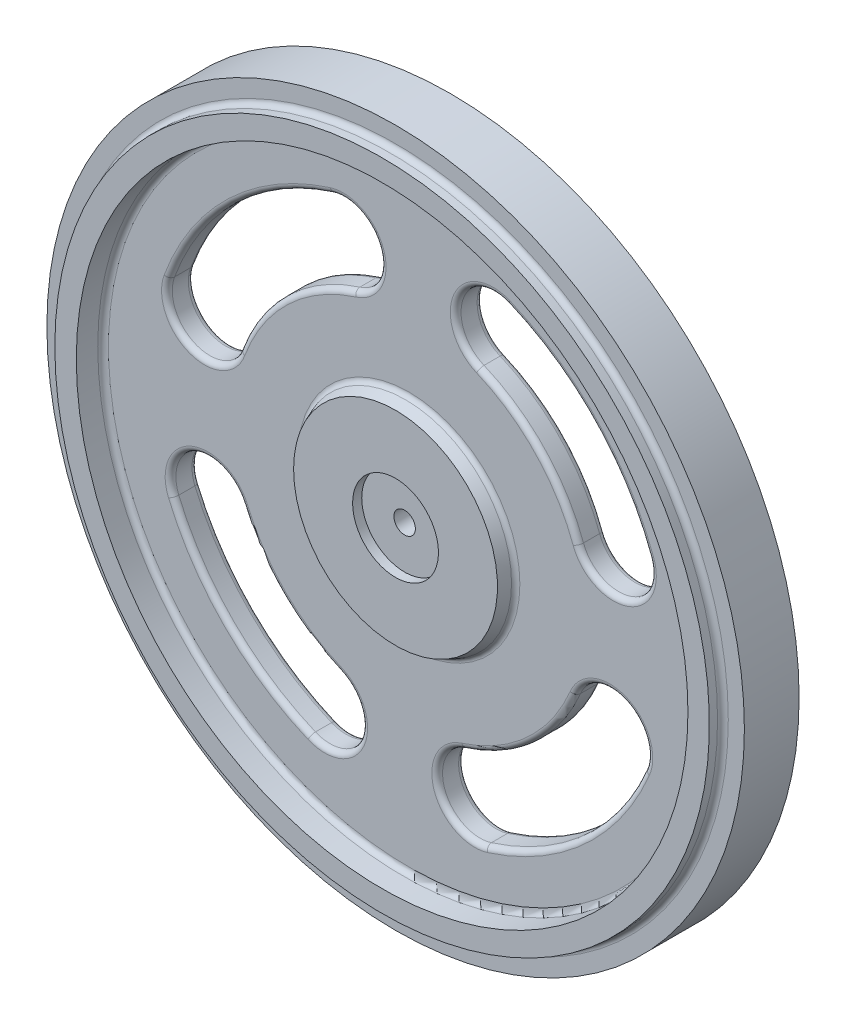
SolidWorks part; units mm, degrees
ref_plane "Front Plane" through (0, 0, 0) normal (0, 0, 1) x (1, 0, 0)
ref_plane "Top Plane" through (0, 0, 0) normal (0, 1, 0) x (1, 0, 0)
ref_plane "Right Plane" through (0, 0, 0) normal (1, 0, 0) x (0, 0, -1)
sketch "Sketch1" plane through (0, 0, 0) normal (1, 0, 0) x (0, 0, -1)
  line L0 (25, 0) -> (-25, 0) construction
  line L1 (-2.55, 32.5) -> (-2.55, 30.5)
  line L2 (-3.81, 28.5) -> (-3.81, 30.5)
  line L3 (-2.55, 32.5) -> (2.55, 32.5)
  line L4 (3.69, 2.75) -> (3.69, 4.5)
  line L5 (-2.55, 30.5) -> (-3.81, 30.5)
  line L6 (2.55, 32.5) -> (2.55, 30.5)
  line L7 (2.55, 30.5) -> (3.69, 30.5)
  line L8 (-3.81, 28.5) -> (-1.31, 28.5)
  line L9 (-1.31, 28.5) -> (-1.31, 10)
  line L10 (1.19, 28.5) -> (1.19, 5)
  line L11 (1.19, 28.5) -> (3.69, 28.5)
  line L12 (3.69, 2.75) -> (-0.16, 2.75)
  line L13 (-0.16, 2.75) -> (-0.16, 1)
  line L14 (-0.16, 1) -> (-1.71, 1)
  line L15 (-1.71, 1) -> (-1.71, 4)
  line L16 (-1.71, 4) -> (-2.56, 4)
  line L17 (3.69, 4.5) -> (1.19, 5)
  line L18 (-1.31, 10) -> (-2.56, 9.5)
  line L19 (-2.56, 9.5) -> (-2.56, 4)
  line L20 (3.69, 28.5) -> (3.69, 30.5)
  dimension "D1" = 7.5
  dimension "D2" = 32.5
  dimension "D3" = 3.81
  dimension "D4" = 50
  dimension "D5" = 5.1
  dimension "D6" = 2.55
  dimension "D7" = 2
  dimension "D8" = 2
  dimension "D9" = 2.5
  dimension "D10" = 2.5
  dimension "D11" = 1.25
  dimension "D12" = 5
  dimension "D13" = 2.75
  dimension "D14" = 3.85
  dimension "D15" = 0.85
  dimension "D16" = 2
  dimension "D17" = 4.5
  dimension "D18" = 9.5
  dimension "D19" = 10
  dimension "D20" = 4
revolve "Revolve1" add sketch "Sketch1" angle 360 about L0
sketch "Sketch2" plane through (0, 0, 1.31) normal (0, 0, 1) x (1, 0, 0)
  arc A0 (-5.0743, 16.0154) -> (-15.7696, 5.7931) centre (0, 0) ccw
  circle A1 centre (0, 0) radius 4 construction
  arc A2 (-7.1885, 22.6884) -> (-22.3403, 8.2069) centre (0, 0) ccw
  circle A3 centre (0, 0) radius 10 construction
  arc A4 (-22.3403, 8.2069) -> (-15.7696, 5.7931) centre (-19.0549, 7) ccw
  arc A5 (15.7696, 5.7931) -> (6.5001, 15.4916) centre (0, 0) ccw
  arc A6 (22.3403, 8.2069) -> (9.2085, 21.9464) centre (0, 0) ccw
  arc A7 (5.0743, -16.0154) -> (15.4916, -6.5001) centre (0, 0) ccw
  arc A8 (7.1885, -22.6884) -> (21.9464, -9.2085) centre (0, 0) ccw
  arc A9 (-15.4916, -6.5001) -> (-6.5001, -15.4916) centre (0, 0) ccw
  arc A10 (-21.9464, -9.2085) -> (-9.2085, -21.9464) centre (0, 0) ccw
  arc A11 (-15.4916, -6.5001) -> (-21.9464, -9.2085) centre (-18.719, -7.8543) ccw
  arc A12 (-9.2085, -21.9464) -> (-6.5001, -15.4916) centre (-7.8543, -18.719) ccw
  arc A13 (-5.0743, 16.0154) -> (-7.1885, 22.6884) centre (-6.1314, 19.3519) ccw
  arc A14 (5.0743, -16.0154) -> (7.1885, -22.6884) centre (6.1314, -19.3519) ccw
  arc A15 (21.9464, -9.2085) -> (15.4916, -6.5001) centre (18.719, -7.8543) ccw
  arc A16 (15.7696, 5.7931) -> (22.3403, 8.2069) centre (19.0549, 7) ccw
  arc A17 (9.2085, 21.9464) -> (6.5001, 15.4916) centre (7.8543, 18.719) ccw
  dimension "D1" = 7
  dimension "D2" = 6.8
  dimension "D3" = 7
  dimension "D4" = 18.719
  dimension "D5" = 7
  dimension "D6" = 18.719
  dimension "D7" = 18.719
  dimension "D8" = 18.719
  dimension "D9" = 14
  dimension "D10" = 14
extrude "Extrude1" cut sketch "Sketch2" against normal up to next
fillet "Fillet1" radius 0.5 38 edges at (-5, 0, -1.19) (-28.5, 0, -1.19) (-11.8794, -11.8794, -1.19) (-4.6269, -20.0732, -1.19) (-16.8291, -16.8291, -1.19) (-20.0732, -4.6269, -1.19) (11.3302, -12.4043, -1.19) (20.0732, -4.6269, -1.19) (16.0511, -17.5728, -1.19) (2.7949, -20.409, -1.19) (-16.4443, 17.2053, -1.19) (-2.7949, 20.409, -1.19) (-11.6078, 12.1449, -1.19) (-20.2618, 3.7147, -1.19) (12.1449, 11.6078, -1.19) (4.6269, 20.0732, -1.19) (17.2053, 16.4443, -1.19) (20.2618, 3.7147, -1.19) (-28.5, 0, 1.31) (-10, 0, 1.31) (-16.8291, -16.8291, 1.31) (-4.6269, -20.0732, 1.31) (-11.8794, -11.8794, 1.31) (-20.0732, -4.6269, 1.31) (16.0511, -17.5728, 1.31) (20.0732, -4.6269, 1.31) (11.3302, -12.4043, 1.31) (2.7949, -20.409, 1.31) (-11.6078, 12.1449, 1.31) (-2.7949, 20.409, 1.31) (-16.4443, 17.2053, 1.31) (-20.2618, 3.7147, 1.31) (17.2053, 16.4443, 1.31) (4.6269, 20.0732, 1.31) (12.1449, 11.6078, 1.31) (20.2618, 3.7147, 1.31) (-28.5, 0, -3.69) (-30.5, 0, 2.55)
sketch "Sketch3" plane through (0, 0, -3.69) normal (0, 0, -1) x (-1, 0, 0)
  line L0 (0, 0) -> (0, 3) construction
  line L1 (0, 0) -> (0.5209, 2.9544) construction
  line L2 (0, 0) -> (0.12, 2.7474) construction
  line L3 (0, 0) -> (0.3589, 2.7265) construction
  line L4 (0.1237, 2.7689) -> (0.1598, 2.9736)
  line L5 (0.3589, 2.7483) -> (0.3589, 2.9562)
  line L6 (0.6027, 2.7053) -> (0.6738, 2.9007)
  line L7 (0.8307, 2.6442) -> (0.8668, 2.849)
  line L8 (1.0633, 2.5596) -> (1.1672, 2.7396)
  line L9 (1.2773, 2.4598) -> (1.3484, 2.6551)
  line L10 (1.4916, 2.3361) -> (1.6252, 2.4953)
  line L11 (1.685, 2.2006) -> (1.789, 2.3807)
  line L12 (1.8746, 2.0415) -> (2.0339, 2.1752)
  line L13 (2.0415, 1.8746) -> (2.1752, 2.0339)
  line L14 (2.2006, 1.685) -> (2.3807, 1.789)
  line L15 (2.3361, 1.4916) -> (2.4953, 1.6252)
  line L16 (2.4598, 1.2773) -> (2.6551, 1.3484)
  line L17 (2.5596, 1.0633) -> (2.7396, 1.1672)
  line L18 (2.6442, 0.8307) -> (2.849, 0.8668)
  line L19 (2.7053, 0.6027) -> (2.9007, 0.6738)
  line L20 (2.7483, 0.3589) -> (2.9562, 0.3589)
  line L21 (2.7689, 0.1237) -> (2.9736, 0.1598)
  line L22 (2.7689, -0.1237) -> (2.9736, -0.1598)
  line L23 (2.7483, -0.3589) -> (2.9562, -0.3589)
  line L24 (2.7053, -0.6027) -> (2.9007, -0.6738)
  line L25 (2.6442, -0.8307) -> (2.849, -0.8668)
  line L26 (2.5596, -1.0633) -> (2.7396, -1.1672)
  line L27 (2.4598, -1.2773) -> (2.6551, -1.3484)
  line L28 (2.3361, -1.4916) -> (2.4953, -1.6252)
  line L29 (2.2006, -1.685) -> (2.3807, -1.789)
  line L30 (2.0415, -1.8746) -> (2.1752, -2.0339)
  line L31 (1.8746, -2.0415) -> (2.0339, -2.1752)
  line L32 (1.685, -2.2006) -> (1.789, -2.3807)
  line L33 (1.4916, -2.3361) -> (1.6252, -2.4953)
  line L34 (1.2773, -2.4598) -> (1.3484, -2.6551)
  line L35 (1.0633, -2.5596) -> (1.1672, -2.7396)
  line L36 (0.8307, -2.6442) -> (0.8668, -2.849)
  line L37 (0.6027, -2.7053) -> (0.6738, -2.9007)
  line L38 (0.3589, -2.7483) -> (0.3589, -2.9562)
  line L39 (0.1237, -2.7689) -> (0.1598, -2.9736)
  line L40 (-0.1237, -2.7689) -> (-0.1598, -2.9736)
  line L41 (-0.3589, -2.7483) -> (-0.3589, -2.9562)
  line L42 (-0.6027, -2.7053) -> (-0.6738, -2.9007)
  line L43 (-0.8307, -2.6442) -> (-0.8668, -2.849)
  line L44 (-1.0633, -2.5596) -> (-1.1672, -2.7396)
  line L45 (-1.2773, -2.4598) -> (-1.3484, -2.6551)
  line L46 (-1.4916, -2.3361) -> (-1.6252, -2.4953)
  line L47 (-1.685, -2.2006) -> (-1.789, -2.3807)
  line L48 (-1.8746, -2.0415) -> (-2.0339, -2.1752)
  line L49 (-2.0415, -1.8746) -> (-2.1752, -2.0339)
  line L50 (-2.2006, -1.685) -> (-2.3807, -1.789)
  line L51 (-2.3361, -1.4916) -> (-2.4953, -1.6252)
  line L52 (-2.4598, -1.2773) -> (-2.6551, -1.3484)
  line L53 (-2.5596, -1.0633) -> (-2.7396, -1.1672)
  line L54 (-2.6442, -0.8307) -> (-2.849, -0.8668)
  line L55 (-2.7053, -0.6027) -> (-2.9007, -0.6738)
  line L56 (-2.7483, -0.3589) -> (-2.9562, -0.3589)
  line L57 (-2.7689, -0.1237) -> (-2.9736, -0.1598)
  line L58 (-2.7689, 0.1237) -> (-2.9736, 0.1598)
  line L59 (-2.7483, 0.3589) -> (-2.9562, 0.3589)
  line L60 (-2.7053, 0.6027) -> (-2.9007, 0.6738)
  line L61 (-2.6442, 0.8307) -> (-2.849, 0.8668)
  line L62 (-2.5596, 1.0633) -> (-2.7396, 1.1672)
  line L63 (-2.4598, 1.2773) -> (-2.6551, 1.3484)
  line L64 (-2.3361, 1.4916) -> (-2.4953, 1.6252)
  line L65 (-2.2006, 1.685) -> (-2.3807, 1.789)
  line L66 (-2.0415, 1.8746) -> (-2.1752, 2.0339)
  line L67 (-1.8746, 2.0415) -> (-2.0339, 2.1752)
  line L68 (-1.685, 2.2006) -> (-1.789, 2.3807)
  line L69 (-1.4916, 2.3361) -> (-1.6252, 2.4953)
  line L70 (-1.2773, 2.4598) -> (-1.3484, 2.6551)
  line L71 (-1.0633, 2.5596) -> (-1.1672, 2.7396)
  line L72 (-0.8307, 2.6442) -> (-0.8668, 2.849)
  line L73 (-0.6027, 2.7053) -> (-0.6738, 2.9007)
  line L74 (-0.3589, 2.7483) -> (-0.3589, 2.9562)
  line L75 (-0.1237, 2.7689) -> (-0.1598, 2.9736)
  circle A0 centre (0, 0) radius 3 construction
  circle A1 centre (0, 0) radius 2.75 construction
  circle A2 centre (0, 0) radius 2.75 construction
  arc A3 (0.186, 2.9942) -> (0.3368, 2.981) centre (0, 0) cw
  arc A4 (0, 2.75) -> (0.0982, 2.7482) centre (0, 0) cw
  arc A5 (0.3805, 2.7236) -> (0.4775, 2.7082) centre (0, 0) cw
  arc A6 (0.1237, 2.7689) -> (0.0982, 2.7482) centre (0.0991, 2.7732) cw
  arc A7 (0.186, 2.9942) -> (0.1598, 2.9736) centre (0.1845, 2.9693) ccw
  arc A8 (0.3368, 2.981) -> (0.3589, 2.9562) centre (0.3339, 2.9562) cw
  arc A9 (0.3589, 2.7483) -> (0.3805, 2.7236) centre (0.3839, 2.7483) ccw
  arc A10 (0.4775, 2.7082) -> (0.574, 2.6894) centre (0, 0) cw
  arc A11 (0.6027, 2.7053) -> (0.574, 2.6894) centre (0.5792, 2.7139) cw
  arc A12 (0.7031, 2.9164) -> (0.6738, 2.9007) centre (0.6973, 2.8921) ccw
  arc A13 (0.7031, 2.9164) -> (0.8493, 2.8773) centre (0, 0) cw
  arc A14 (0.8493, 2.8773) -> (0.8668, 2.849) centre (0.8422, 2.8533) cw
  arc A15 (0.8307, 2.6442) -> (0.8476, 2.6161) centre (0.8554, 2.6399) ccw
  arc A16 (0.8476, 2.6161) -> (0.9406, 2.5842) centre (0, 0) cw
  arc A17 (0.9406, 2.5842) -> (1.0323, 2.5489) centre (0, 0) cw
  arc A18 (1.0633, 2.5596) -> (1.0323, 2.5489) centre (1.0416, 2.5721) cw
  arc A19 (1.1989, 2.75) -> (1.1672, 2.7396) centre (1.1889, 2.7271) ccw
  arc A20 (1.1989, 2.75) -> (1.336, 2.6861) centre (0, 0) cw
  arc A21 (1.336, 2.6861) -> (1.3484, 2.6551) centre (1.3249, 2.6637) cw
  arc A22 (1.2773, 2.4598) -> (1.2891, 2.4292) centre (1.3008, 2.4512) ccw
  arc A23 (1.2891, 2.4292) -> (1.375, 2.3816) centre (0, 0) cw
  arc A24 (1.375, 2.3816) -> (1.4592, 2.3309) centre (0, 0) cw
  arc A25 (1.4916, 2.3361) -> (1.4592, 2.3309) centre (1.4725, 2.3521) cw
  arc A26 (1.6582, 2.5001) -> (1.6252, 2.4953) centre (1.6444, 2.4792) ccw
  arc A27 (1.6582, 2.5001) -> (1.7822, 2.4133) centre (0, 0) cw
  arc A28 (1.7822, 2.4133) -> (1.789, 2.3807) centre (1.7673, 2.3932) cw
  arc A29 (1.685, 2.2006) -> (1.6913, 2.1684) centre (1.7067, 2.1881) ccw
  arc A30 (1.6913, 2.1684) -> (1.7677, 2.1066) centre (0, 0) cw
  arc A31 (1.7677, 2.1066) -> (1.8418, 2.0421) centre (0, 0) cw
  arc A32 (1.8746, 2.0415) -> (1.8418, 2.0421) centre (1.8585, 2.0607) cw
  arc A33 (2.0671, 2.1741) -> (2.0339, 2.1752) centre (2.0499, 2.156) ccw
  arc A34 (2.0671, 2.1741) -> (2.1741, 2.0671) centre (0, 0) cw
  arc A35 (2.1741, 2.0671) -> (2.1752, 2.0339) centre (2.156, 2.0499) cw
  arc A36 (2.0415, 1.8746) -> (2.0421, 1.8418) centre (2.0607, 1.8585) ccw
  arc A37 (2.0421, 1.8418) -> (2.1066, 1.7677) centre (0, 0) cw
  arc A38 (2.1066, 1.7677) -> (2.1684, 1.6913) centre (0, 0) cw
  arc A39 (2.2006, 1.685) -> (2.1684, 1.6913) centre (2.1881, 1.7067) cw
  arc A40 (2.4133, 1.7822) -> (2.3807, 1.789) centre (2.3932, 1.7673) ccw
  arc A41 (2.4133, 1.7822) -> (2.5001, 1.6582) centre (0, 0) cw
  arc A42 (2.5001, 1.6582) -> (2.4953, 1.6252) centre (2.4792, 1.6444) cw
  arc A43 (2.3361, 1.4916) -> (2.3309, 1.4592) centre (2.3521, 1.4725) ccw
  arc A44 (2.3309, 1.4592) -> (2.3816, 1.375) centre (0, 0) cw
  arc A45 (2.3816, 1.375) -> (2.4292, 1.2891) centre (0, 0) cw
  arc A46 (2.4598, 1.2773) -> (2.4292, 1.2891) centre (2.4512, 1.3008) cw
  arc A47 (2.6861, 1.336) -> (2.6551, 1.3484) centre (2.6637, 1.3249) ccw
  arc A48 (2.6861, 1.336) -> (2.75, 1.1989) centre (0, 0) cw
  arc A49 (2.75, 1.1989) -> (2.7396, 1.1672) centre (2.7271, 1.1889) cw
  arc A50 (2.5596, 1.0633) -> (2.5489, 1.0323) centre (2.5721, 1.0416) ccw
  arc A51 (2.5489, 1.0323) -> (2.5842, 0.9406) centre (0, 0) cw
  arc A52 (2.5842, 0.9406) -> (2.6161, 0.8476) centre (0, 0) cw
  arc A53 (2.6442, 0.8307) -> (2.6161, 0.8476) centre (2.6399, 0.8554) cw
  arc A54 (2.8773, 0.8493) -> (2.849, 0.8668) centre (2.8533, 0.8422) ccw
  arc A55 (2.8773, 0.8493) -> (2.9164, 0.7031) centre (0, 0) cw
  arc A56 (2.9164, 0.7031) -> (2.9007, 0.6738) centre (2.8921, 0.6973) cw
  arc A57 (2.7053, 0.6027) -> (2.6894, 0.574) centre (2.7139, 0.5792) ccw
  arc A58 (2.6894, 0.574) -> (2.7082, 0.4775) centre (0, 0) cw
  arc A59 (2.7082, 0.4775) -> (2.7236, 0.3805) centre (0, 0) cw
  arc A60 (2.7483, 0.3589) -> (2.7236, 0.3805) centre (2.7483, 0.3839) cw
  arc A61 (2.981, 0.3368) -> (2.9562, 0.3589) centre (2.9562, 0.3339) ccw
  arc A62 (2.981, 0.3368) -> (2.9942, 0.186) centre (0, 0) cw
  arc A63 (2.9942, 0.186) -> (2.9736, 0.1598) centre (2.9693, 0.1845) cw
  arc A64 (2.7689, 0.1237) -> (2.7482, 0.0982) centre (2.7732, 0.0991) ccw
  arc A65 (2.7482, 0.0982) -> (2.75, 0) centre (0, 0) cw
  arc A66 (2.75, 0) -> (2.7482, -0.0982) centre (0, 0) cw
  arc A67 (2.7689, -0.1237) -> (2.7482, -0.0982) centre (2.7732, -0.0991) cw
  arc A68 (2.9942, -0.186) -> (2.9736, -0.1598) centre (2.9693, -0.1845) ccw
  arc A69 (2.9942, -0.186) -> (2.981, -0.3368) centre (0, 0) cw
  arc A70 (2.981, -0.3368) -> (2.9562, -0.3589) centre (2.9562, -0.3339) cw
  arc A71 (2.7483, -0.3589) -> (2.7236, -0.3805) centre (2.7483, -0.3839) ccw
  arc A72 (2.7236, -0.3805) -> (2.7082, -0.4775) centre (0, 0) cw
  arc A73 (2.7082, -0.4775) -> (2.6894, -0.574) centre (0, 0) cw
  arc A74 (2.7053, -0.6027) -> (2.6894, -0.574) centre (2.7139, -0.5792) cw
  arc A75 (2.9164, -0.7031) -> (2.9007, -0.6738) centre (2.8921, -0.6973) ccw
  arc A76 (2.9164, -0.7031) -> (2.8773, -0.8493) centre (0, 0) cw
  arc A77 (2.8773, -0.8493) -> (2.849, -0.8668) centre (2.8533, -0.8422) cw
  arc A78 (2.6442, -0.8307) -> (2.6161, -0.8476) centre (2.6399, -0.8554) ccw
  arc A79 (2.6161, -0.8476) -> (2.5842, -0.9406) centre (0, 0) cw
  arc A80 (2.5842, -0.9406) -> (2.5489, -1.0323) centre (0, 0) cw
  arc A81 (2.5596, -1.0633) -> (2.5489, -1.0323) centre (2.5721, -1.0416) cw
  arc A82 (2.75, -1.1989) -> (2.7396, -1.1672) centre (2.7271, -1.1889) ccw
  arc A83 (2.75, -1.1989) -> (2.6861, -1.336) centre (0, 0) cw
  arc A84 (2.6861, -1.336) -> (2.6551, -1.3484) centre (2.6637, -1.3249) cw
  arc A85 (2.4598, -1.2773) -> (2.4292, -1.2891) centre (2.4512, -1.3008) ccw
  arc A86 (2.4292, -1.2891) -> (2.3816, -1.375) centre (0, 0) cw
  arc A87 (2.3816, -1.375) -> (2.3309, -1.4592) centre (0, 0) cw
  arc A88 (2.3361, -1.4916) -> (2.3309, -1.4592) centre (2.3521, -1.4725) cw
  arc A89 (2.5001, -1.6582) -> (2.4953, -1.6252) centre (2.4792, -1.6444) ccw
  arc A90 (2.5001, -1.6582) -> (2.4133, -1.7822) centre (0, 0) cw
  arc A91 (2.4133, -1.7822) -> (2.3807, -1.789) centre (2.3932, -1.7673) cw
  arc A92 (2.2006, -1.685) -> (2.1684, -1.6913) centre (2.1881, -1.7067) ccw
  arc A93 (2.1684, -1.6913) -> (2.1066, -1.7677) centre (0, 0) cw
  arc A94 (2.1066, -1.7677) -> (2.0421, -1.8418) centre (0, 0) cw
  arc A95 (2.0415, -1.8746) -> (2.0421, -1.8418) centre (2.0607, -1.8585) cw
  arc A96 (2.1741, -2.0671) -> (2.1752, -2.0339) centre (2.156, -2.0499) ccw
  arc A97 (2.1741, -2.0671) -> (2.0671, -2.1741) centre (0, 0) cw
  arc A98 (2.0671, -2.1741) -> (2.0339, -2.1752) centre (2.0499, -2.156) cw
  arc A99 (1.8746, -2.0415) -> (1.8418, -2.0421) centre (1.8585, -2.0607) ccw
  arc A100 (1.8418, -2.0421) -> (1.7677, -2.1066) centre (0, 0) cw
  arc A101 (1.7677, -2.1066) -> (1.6913, -2.1684) centre (0, 0) cw
  arc A102 (1.685, -2.2006) -> (1.6913, -2.1684) centre (1.7067, -2.1881) cw
  arc A103 (1.7822, -2.4133) -> (1.789, -2.3807) centre (1.7673, -2.3932) ccw
  arc A104 (1.7822, -2.4133) -> (1.6582, -2.5001) centre (0, 0) cw
  arc A105 (1.6582, -2.5001) -> (1.6252, -2.4953) centre (1.6444, -2.4792) cw
  arc A106 (1.4916, -2.3361) -> (1.4592, -2.3309) centre (1.4725, -2.3521) ccw
  arc A107 (1.4592, -2.3309) -> (1.375, -2.3816) centre (0, 0) cw
  arc A108 (1.375, -2.3816) -> (1.2891, -2.4292) centre (0, 0) cw
  arc A109 (1.2773, -2.4598) -> (1.2891, -2.4292) centre (1.3008, -2.4512) cw
  arc A110 (1.336, -2.6861) -> (1.3484, -2.6551) centre (1.3249, -2.6637) ccw
  arc A111 (1.336, -2.6861) -> (1.1989, -2.75) centre (0, 0) cw
  arc A112 (1.1989, -2.75) -> (1.1672, -2.7396) centre (1.1889, -2.7271) cw
  arc A113 (1.0633, -2.5596) -> (1.0323, -2.5489) centre (1.0416, -2.5721) ccw
  arc A114 (1.0323, -2.5489) -> (0.9406, -2.5842) centre (0, 0) cw
  arc A115 (0.9406, -2.5842) -> (0.8476, -2.6161) centre (0, 0) cw
  arc A116 (0.8307, -2.6442) -> (0.8476, -2.6161) centre (0.8554, -2.6399) cw
  arc A117 (0.8493, -2.8773) -> (0.8668, -2.849) centre (0.8422, -2.8533) ccw
  arc A118 (0.8493, -2.8773) -> (0.7031, -2.9164) centre (0, 0) cw
  arc A119 (0.7031, -2.9164) -> (0.6738, -2.9007) centre (0.6973, -2.8921) cw
  arc A120 (0.6027, -2.7053) -> (0.574, -2.6894) centre (0.5792, -2.7139) ccw
  arc A121 (0.574, -2.6894) -> (0.4775, -2.7082) centre (0, 0) cw
  arc A122 (0.4775, -2.7082) -> (0.3805, -2.7236) centre (0, 0) cw
  arc A123 (0.3589, -2.7483) -> (0.3805, -2.7236) centre (0.3839, -2.7483) cw
  arc A124 (0.3368, -2.981) -> (0.3589, -2.9562) centre (0.3339, -2.9562) ccw
  arc A125 (0.3368, -2.981) -> (0.186, -2.9942) centre (0, 0) cw
  arc A126 (0.186, -2.9942) -> (0.1598, -2.9736) centre (0.1845, -2.9693) cw
  arc A127 (0.1237, -2.7689) -> (0.0982, -2.7482) centre (0.0991, -2.7732) ccw
  arc A128 (0.0982, -2.7482) -> (0, -2.75) centre (0, 0) cw
  arc A129 (0, -2.75) -> (-0.0982, -2.7482) centre (0, 0) cw
  arc A130 (-0.1237, -2.7689) -> (-0.0982, -2.7482) centre (-0.0991, -2.7732) cw
  arc A131 (-0.186, -2.9942) -> (-0.1598, -2.9736) centre (-0.1845, -2.9693) ccw
  arc A132 (-0.186, -2.9942) -> (-0.3368, -2.981) centre (0, 0) cw
  arc A133 (-0.3368, -2.981) -> (-0.3589, -2.9562) centre (-0.3339, -2.9562) cw
  arc A134 (-0.3589, -2.7483) -> (-0.3805, -2.7236) centre (-0.3839, -2.7483) ccw
  arc A135 (-0.3805, -2.7236) -> (-0.4775, -2.7082) centre (0, 0) cw
  arc A136 (-0.4775, -2.7082) -> (-0.574, -2.6894) centre (0, 0) cw
  arc A137 (-0.6027, -2.7053) -> (-0.574, -2.6894) centre (-0.5792, -2.7139) cw
  arc A138 (-0.7031, -2.9164) -> (-0.6738, -2.9007) centre (-0.6973, -2.8921) ccw
  arc A139 (-0.7031, -2.9164) -> (-0.8493, -2.8773) centre (0, 0) cw
  arc A140 (-0.8493, -2.8773) -> (-0.8668, -2.849) centre (-0.8422, -2.8533) cw
  arc A141 (-0.8307, -2.6442) -> (-0.8476, -2.6161) centre (-0.8554, -2.6399) ccw
  arc A142 (-0.8476, -2.6161) -> (-0.9406, -2.5842) centre (0, 0) cw
  arc A143 (-0.9406, -2.5842) -> (-1.0323, -2.5489) centre (0, 0) cw
  arc A144 (-1.0633, -2.5596) -> (-1.0323, -2.5489) centre (-1.0416, -2.5721) cw
  arc A145 (-1.1989, -2.75) -> (-1.1672, -2.7396) centre (-1.1889, -2.7271) ccw
  arc A146 (-1.1989, -2.75) -> (-1.336, -2.6861) centre (0, 0) cw
  arc A147 (-1.336, -2.6861) -> (-1.3484, -2.6551) centre (-1.3249, -2.6637) cw
  arc A148 (-1.2773, -2.4598) -> (-1.2891, -2.4292) centre (-1.3008, -2.4512) ccw
  arc A149 (-1.2891, -2.4292) -> (-1.375, -2.3816) centre (0, 0) cw
  arc A150 (-1.375, -2.3816) -> (-1.4592, -2.3309) centre (0, 0) cw
  arc A151 (-1.4916, -2.3361) -> (-1.4592, -2.3309) centre (-1.4725, -2.3521) cw
  arc A152 (-1.6582, -2.5001) -> (-1.6252, -2.4953) centre (-1.6444, -2.4792) ccw
  arc A153 (-1.6582, -2.5001) -> (-1.7822, -2.4133) centre (0, 0) cw
  arc A154 (-1.7822, -2.4133) -> (-1.789, -2.3807) centre (-1.7673, -2.3932) cw
  arc A155 (-1.685, -2.2006) -> (-1.6913, -2.1684) centre (-1.7067, -2.1881) ccw
  arc A156 (-1.6913, -2.1684) -> (-1.7677, -2.1066) centre (0, 0) cw
  arc A157 (-1.7677, -2.1066) -> (-1.8418, -2.0421) centre (0, 0) cw
  arc A158 (-1.8746, -2.0415) -> (-1.8418, -2.0421) centre (-1.8585, -2.0607) cw
  arc A159 (-2.0671, -2.1741) -> (-2.0339, -2.1752) centre (-2.0499, -2.156) ccw
  arc A160 (-2.0671, -2.1741) -> (-2.1741, -2.0671) centre (0, 0) cw
  arc A161 (-2.1741, -2.0671) -> (-2.1752, -2.0339) centre (-2.156, -2.0499) cw
  arc A162 (-2.0415, -1.8746) -> (-2.0421, -1.8418) centre (-2.0607, -1.8585) ccw
  arc A163 (-2.0421, -1.8418) -> (-2.1066, -1.7677) centre (0, 0) cw
  arc A164 (-2.1066, -1.7677) -> (-2.1684, -1.6913) centre (0, 0) cw
  arc A165 (-2.2006, -1.685) -> (-2.1684, -1.6913) centre (-2.1881, -1.7067) cw
  arc A166 (-2.4133, -1.7822) -> (-2.3807, -1.789) centre (-2.3932, -1.7673) ccw
  arc A167 (-2.4133, -1.7822) -> (-2.5001, -1.6582) centre (0, 0) cw
  arc A168 (-2.5001, -1.6582) -> (-2.4953, -1.6252) centre (-2.4792, -1.6444) cw
  arc A169 (-2.3361, -1.4916) -> (-2.3309, -1.4592) centre (-2.3521, -1.4725) ccw
  arc A170 (-2.3309, -1.4592) -> (-2.3816, -1.375) centre (0, 0) cw
  arc A171 (-2.3816, -1.375) -> (-2.4292, -1.2891) centre (0, 0) cw
  arc A172 (-2.4598, -1.2773) -> (-2.4292, -1.2891) centre (-2.4512, -1.3008) cw
  arc A173 (-2.6861, -1.336) -> (-2.6551, -1.3484) centre (-2.6637, -1.3249) ccw
  arc A174 (-2.6861, -1.336) -> (-2.75, -1.1989) centre (0, 0) cw
  arc A175 (-2.75, -1.1989) -> (-2.7396, -1.1672) centre (-2.7271, -1.1889) cw
  arc A176 (-2.5596, -1.0633) -> (-2.5489, -1.0323) centre (-2.5721, -1.0416) ccw
  arc A177 (-2.5489, -1.0323) -> (-2.5842, -0.9406) centre (0, 0) cw
  arc A178 (-2.5842, -0.9406) -> (-2.6161, -0.8476) centre (0, 0) cw
  arc A179 (-2.6442, -0.8307) -> (-2.6161, -0.8476) centre (-2.6399, -0.8554) cw
  arc A180 (-2.8773, -0.8493) -> (-2.849, -0.8668) centre (-2.8533, -0.8422) ccw
  arc A181 (-2.8773, -0.8493) -> (-2.9164, -0.7031) centre (0, 0) cw
  arc A182 (-2.9164, -0.7031) -> (-2.9007, -0.6738) centre (-2.8921, -0.6973) cw
  arc A183 (-2.7053, -0.6027) -> (-2.6894, -0.574) centre (-2.7139, -0.5792) ccw
  arc A184 (-2.6894, -0.574) -> (-2.7082, -0.4775) centre (0, 0) cw
  arc A185 (-2.7082, -0.4775) -> (-2.7236, -0.3805) centre (0, 0) cw
  arc A186 (-2.7483, -0.3589) -> (-2.7236, -0.3805) centre (-2.7483, -0.3839) cw
  arc A187 (-2.981, -0.3368) -> (-2.9562, -0.3589) centre (-2.9562, -0.3339) ccw
  arc A188 (-2.981, -0.3368) -> (-2.9942, -0.186) centre (0, 0) cw
  arc A189 (-2.9942, -0.186) -> (-2.9736, -0.1598) centre (-2.9693, -0.1845) cw
  arc A190 (-2.7689, -0.1237) -> (-2.7482, -0.0982) centre (-2.7732, -0.0991) ccw
  arc A191 (-2.7482, -0.0982) -> (-2.75, 0) centre (0, 0) cw
  arc A192 (-2.75, 0) -> (-2.7482, 0.0982) centre (0, 0) cw
  arc A193 (-2.7689, 0.1237) -> (-2.7482, 0.0982) centre (-2.7732, 0.0991) cw
  arc A194 (-2.9942, 0.186) -> (-2.9736, 0.1598) centre (-2.9693, 0.1845) ccw
  arc A195 (-2.9942, 0.186) -> (-2.981, 0.3368) centre (0, 0) cw
  arc A196 (-2.981, 0.3368) -> (-2.9562, 0.3589) centre (-2.9562, 0.3339) cw
  arc A197 (-2.7483, 0.3589) -> (-2.7236, 0.3805) centre (-2.7483, 0.3839) ccw
  arc A198 (-2.7236, 0.3805) -> (-2.7082, 0.4775) centre (0, 0) cw
  arc A199 (-2.7082, 0.4775) -> (-2.6894, 0.574) centre (0, 0) cw
  arc A200 (-2.7053, 0.6027) -> (-2.6894, 0.574) centre (-2.7139, 0.5792) cw
  arc A201 (-2.9164, 0.7031) -> (-2.9007, 0.6738) centre (-2.8921, 0.6973) ccw
  arc A202 (-2.9164, 0.7031) -> (-2.8773, 0.8493) centre (0, 0) cw
  arc A203 (-2.8773, 0.8493) -> (-2.849, 0.8668) centre (-2.8533, 0.8422) cw
  arc A204 (-2.6442, 0.8307) -> (-2.6161, 0.8476) centre (-2.6399, 0.8554) ccw
  arc A205 (-2.6161, 0.8476) -> (-2.5842, 0.9406) centre (0, 0) cw
  arc A206 (-2.5842, 0.9406) -> (-2.5489, 1.0323) centre (0, 0) cw
  arc A207 (-2.5596, 1.0633) -> (-2.5489, 1.0323) centre (-2.5721, 1.0416) cw
  arc A208 (-2.75, 1.1989) -> (-2.7396, 1.1672) centre (-2.7271, 1.1889) ccw
  arc A209 (-2.75, 1.1989) -> (-2.6861, 1.336) centre (0, 0) cw
  arc A210 (-2.6861, 1.336) -> (-2.6551, 1.3484) centre (-2.6637, 1.3249) cw
  arc A211 (-2.4598, 1.2773) -> (-2.4292, 1.2891) centre (-2.4512, 1.3008) ccw
  arc A212 (-2.4292, 1.2891) -> (-2.3816, 1.375) centre (0, 0) cw
  arc A213 (-2.3816, 1.375) -> (-2.3309, 1.4592) centre (0, 0) cw
  arc A214 (-2.3361, 1.4916) -> (-2.3309, 1.4592) centre (-2.3521, 1.4725) cw
  arc A215 (-2.5001, 1.6582) -> (-2.4953, 1.6252) centre (-2.4792, 1.6444) ccw
  arc A216 (-2.5001, 1.6582) -> (-2.4133, 1.7822) centre (0, 0) cw
  arc A217 (-2.4133, 1.7822) -> (-2.3807, 1.789) centre (-2.3932, 1.7673) cw
  arc A218 (-2.2006, 1.685) -> (-2.1684, 1.6913) centre (-2.1881, 1.7067) ccw
  arc A219 (-2.1684, 1.6913) -> (-2.1066, 1.7677) centre (0, 0) cw
  arc A220 (-2.1066, 1.7677) -> (-2.0421, 1.8418) centre (0, 0) cw
  arc A221 (-2.0415, 1.8746) -> (-2.0421, 1.8418) centre (-2.0607, 1.8585) cw
  arc A222 (-2.1741, 2.0671) -> (-2.1752, 2.0339) centre (-2.156, 2.0499) ccw
  arc A223 (-2.1741, 2.0671) -> (-2.0671, 2.1741) centre (0, 0) cw
  arc A224 (-2.0671, 2.1741) -> (-2.0339, 2.1752) centre (-2.0499, 2.156) cw
  arc A225 (-1.8746, 2.0415) -> (-1.8418, 2.0421) centre (-1.8585, 2.0607) ccw
  arc A226 (-1.8418, 2.0421) -> (-1.7677, 2.1066) centre (0, 0) cw
  arc A227 (-1.7677, 2.1066) -> (-1.6913, 2.1684) centre (0, 0) cw
  arc A228 (-1.685, 2.2006) -> (-1.6913, 2.1684) centre (-1.7067, 2.1881) cw
  arc A229 (-1.7822, 2.4133) -> (-1.789, 2.3807) centre (-1.7673, 2.3932) ccw
  arc A230 (-1.7822, 2.4133) -> (-1.6582, 2.5001) centre (0, 0) cw
  arc A231 (-1.6582, 2.5001) -> (-1.6252, 2.4953) centre (-1.6444, 2.4792) cw
  arc A232 (-1.4916, 2.3361) -> (-1.4592, 2.3309) centre (-1.4725, 2.3521) ccw
  arc A233 (-1.4592, 2.3309) -> (-1.375, 2.3816) centre (0, 0) cw
  arc A234 (-1.375, 2.3816) -> (-1.2891, 2.4292) centre (0, 0) cw
  arc A235 (-1.2773, 2.4598) -> (-1.2891, 2.4292) centre (-1.3008, 2.4512) cw
  arc A236 (-1.336, 2.6861) -> (-1.3484, 2.6551) centre (-1.3249, 2.6637) ccw
  arc A237 (-1.336, 2.6861) -> (-1.1989, 2.75) centre (0, 0) cw
  arc A238 (-1.1989, 2.75) -> (-1.1672, 2.7396) centre (-1.1889, 2.7271) cw
  arc A239 (-1.0633, 2.5596) -> (-1.0323, 2.5489) centre (-1.0416, 2.5721) ccw
  arc A240 (-1.0323, 2.5489) -> (-0.9406, 2.5842) centre (0, 0) cw
  arc A241 (-0.9406, 2.5842) -> (-0.8476, 2.6161) centre (0, 0) cw
  arc A242 (-0.8307, 2.6442) -> (-0.8476, 2.6161) centre (-0.8554, 2.6399) cw
  arc A243 (-0.8493, 2.8773) -> (-0.8668, 2.849) centre (-0.8422, 2.8533) ccw
  arc A244 (-0.8493, 2.8773) -> (-0.7031, 2.9164) centre (0, 0) cw
  arc A245 (-0.7031, 2.9164) -> (-0.6738, 2.9007) centre (-0.6973, 2.8921) cw
  arc A246 (-0.6027, 2.7053) -> (-0.574, 2.6894) centre (-0.5792, 2.7139) ccw
  arc A247 (-0.574, 2.6894) -> (-0.4775, 2.7082) centre (0, 0) cw
  arc A248 (-0.4775, 2.7082) -> (-0.3805, 2.7236) centre (0, 0) cw
  arc A249 (-0.3589, 2.7483) -> (-0.3805, 2.7236) centre (-0.3839, 2.7483) cw
  arc A250 (-0.3368, 2.981) -> (-0.3589, 2.9562) centre (-0.3339, 2.9562) ccw
  arc A251 (-0.3368, 2.981) -> (-0.186, 2.9942) centre (0, 0) cw
  arc A252 (-0.186, 2.9942) -> (-0.1598, 2.9736) centre (-0.1845, 2.9693) cw
  arc A253 (-0.1237, 2.7689) -> (-0.0982, 2.7482) centre (-0.0991, 2.7732) ccw
  arc A254 (-0.0982, 2.7482) -> (0, 2.75) centre (0, 0) cw
  point P22 (0.1637, 2.9955)
  point P25 (0.3589, 2.9784)
  dimension "D1" = 6
  dimension "D7" = 0.025
  dimension "D2" = 10
  dimension "D3" = 2.5
  dimension "D4" = 2.5
  dimension "D5" = 10
  dimension "D6" = 10
extrude "Extrude2" cut sketch "Sketch3" against normal up to surface (3.85 mm away) up to face at (-2.75, 0, 0.16)
